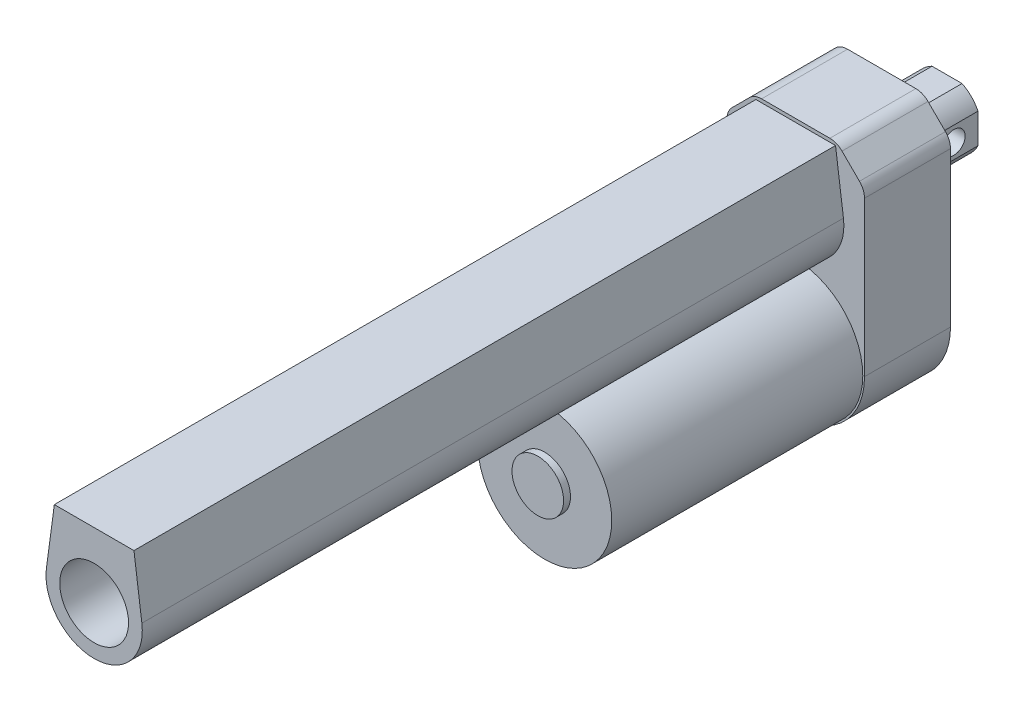
SolidWorks part; units mm, degrees
ref_plane "前视基准面" through (0, 0, 0) normal (0, 0, 1) x (1, 0, 0)
ref_plane "上视基准面" through (0, 0, 0) normal (0, 1, 0) x (1, 0, 0)
ref_plane "右视基准面" through (0, 0, 0) normal (1, 0, 0) x (0, 0, -1)
sketch "草图1" plane through (0, 0, 0) normal (0, 0, 1) x (1, 0, 0)
  line L0 (-20, 0) -> (-20, 44.9289)
  line L1 (-9.9289, 55) -> (9.9289, 55)
  line L2 (20, 44.9289) -> (20, 0)
  line L3 (-18.5355, 48.4645) -> (-13.4645, 53.5355)
  line L4 (13.4645, 53.5355) -> (18.5355, 48.4645)
  arc A0 (-20, 0) -> (20, 0) centre (0, 0) ccw
  arc A1 (-20, 44.9289) -> (-18.5355, 48.4645) centre (-15, 44.9289) cw
  arc A2 (20, 44.9289) -> (18.5355, 48.4645) centre (15, 44.9289) ccw
  arc A3 (13.4645, 53.5355) -> (9.9289, 55) centre (9.9289, 50) ccw
  arc A4 (-13.4645, 53.5355) -> (-9.9289, 55) centre (-9.9289, 50) cw
  point P4 (-20, 55)
  point P6 (20, 55)
  point P13 (-20, 47)
  point P16 (20, 47)
  point P19 (12, 55)
  point P22 (-12, 55)
  dimension "D1" = 40
  dimension "D2" = 55
  dimension "D3" = 5
  dimension "D4" = 5
extrude "凸台-拉伸1" add sketch "草图1" along normal blind 25
sketch "草图2" plane through (0, 0, 25) normal (0, 0, 1) x (1, 0, 0)
  circle A0 centre (0, 0) radius 19.5
  dimension "D1" = 39
extrude "凸台-拉伸2" add sketch "草图2" along normal blind 73
sketch "草图3" plane through (0, 0, 98) normal (0, 0, 1) x (1, 0, 0)
  circle A0 centre (0, 0) radius 7.5
  dimension "D1" = 15
extrude "凸台-拉伸3" add sketch "草图3" along normal blind 2
sketch "草图4" plane through (0, 0, 25) normal (0, 0, 1) x (1, 0, 0)
  line L0 (9.9289, 55) -> (-9.9289, 55) construction
  line L1 (-11.5765, 54) -> (-13.8757, 36.8615)
  line L3 (11.5765, 54) -> (13.8757, 36.8615)
  line L6 (0, 20.7202) -> (0, 56.7049) construction
  line L7 (-20, 44.9289) -> (-20, 0) construction
  line L8 (20, 0) -> (20, 44.9289) construction
  line L9 (-11.5765, 54) -> (11.5765, 54)
  arc A0 (-13.8757, 36.8615) -> (13.8757, 36.8615) centre (0, 35) ccw
  dimension "D1" = 28
  dimension "D2" = 20
  dimension "D3" = 1
extrude "凸台-拉伸4" add sketch "草图4" along normal blind 204
sketch "草图5" plane through (0, 0, 229) normal (0, 0, 1) x (1, 0, 0)
  circle A0 centre (0, 35) radius 10
  dimension "D1" = 20
extrude "切除-拉伸1" cut sketch "草图5" against normal blind 410
sketch "草图6" plane through (0, 0, 0) normal (0, 0, -1) x (-1, 0, 0)
  line L0 (-30.2846, 35) -> (34.2706, 35) construction
  line L1 (0, 69.8123) -> (0, -26.886) construction
  line L2 (-9.9289, 55) -> (9.9289, 55) construction
  line L4 (-4.3589, 44) -> (4.3589, 44)
  line L5 (-9, 39.3589) -> (-9, 30.6411)
  line L6 (-4.3589, 26) -> (4.3589, 26)
  line L7 (9, 39.3589) -> (9, 30.6411)
  arc A0 (-4.3589, 44) -> (-9, 39.3589) centre (0, 35) ccw
  arc A1 (9, 39.3589) -> (4.3589, 44) centre (0, 35) ccw
  arc A2 (-9, 30.6411) -> (-4.3589, 26) centre (0, 35) ccw
  arc A3 (4.3589, 26) -> (9, 30.6411) centre (0, 35) ccw
  dimension "D3" = 20
  dimension "D1" = 20
  dimension "D2" = 18
  dimension "D4" = 18
extrude "凸台-拉伸5" add sketch "草图6" along normal blind 19
sketch "草图7" plane through (9, 0, 0) normal (1, 0, 0) x (0, 0, -1)
  line L0 (26.7064, 35) -> (-8.4403, 35) construction
  line L2 (19, 44) -> (0, 44) construction
  line L3 (19, 26) -> (0, 26) construction
  line L4 (19, 39.3589) -> (19, 30.6411) construction
  circle A0 centre (12, 35) radius 3.25
  dimension "D1" = 6.5
  dimension "D2" = 7
extrude "切除-拉伸2" cut sketch "草图7" against normal blind 20
